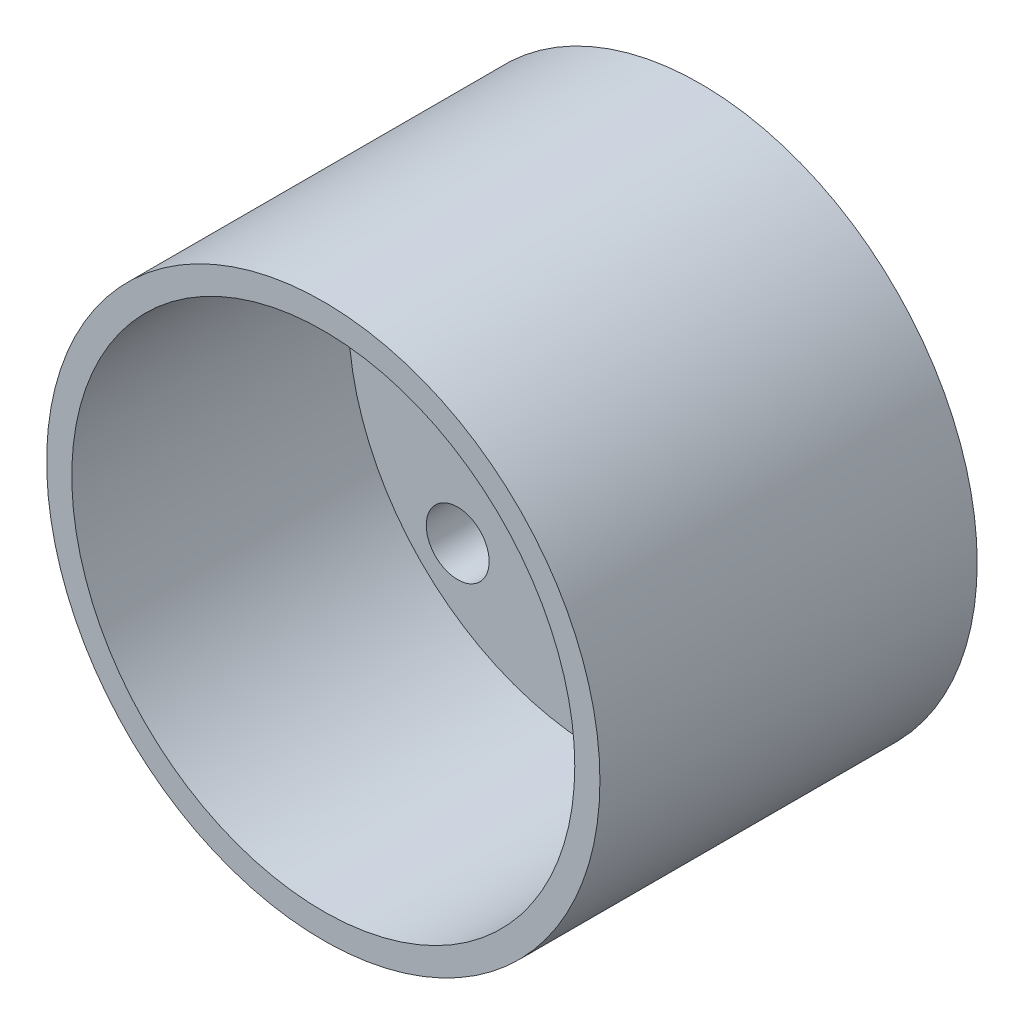
SolidWorks part; units mm, degrees
ref_plane "Front Plane" through (0, 0, 0) normal (0, 0, 1) x (1, 0, 0)
ref_plane "Top Plane" through (0, 0, 0) normal (0, 1, 0) x (1, 0, 0)
ref_plane "Right Plane" through (0, 0, 0) normal (1, 0, 0) x (0, 0, -1)
sketch "Sketch1" plane through (0, 0, 0) normal (0, 0, 1) x (1, 0, 0)
  circle A0 centre (0, 0) radius 11
  dimension "D1" = 22
extrude "Boss-Extrude1" add sketch "Sketch1" along normal blind 15
sketch "Sketch3" plane through (0, 0, 15) normal (0, 0, 1) x (1, 0, 0)
  circle A0 centre (0, 0) radius 10
  dimension "D1" = 20
extrude "Cut-Extrude1" cut sketch "Sketch3" against normal blind 11
sketch "Sketch4" plane through (0, 0, 0) normal (0, 0, -1) x (-1, 0, 0)
  circle A0 centre (0, 0) radius 4.15
  circle A1 centre (0, 8) radius 1.25
  circle A2 centre (5.6569, 5.6569) radius 1.25
  circle A3 centre (8, 0) radius 1.25
  circle A4 centre (5.6569, -5.6569) radius 1.25
  circle A5 centre (0, -8) radius 1.25
  circle A6 centre (-5.6569, -5.6569) radius 1.25
  circle A7 centre (-8, 0) radius 1.25
  circle A8 centre (-5.6569, 5.6569) radius 1.25
  point P22 (0, 0)
  dimension "D1" = 8.3
  dimension "D2" = 2.5
  dimension "D3" = 8
  dimension "D4" = 8
extrude "Cut-Extrude2" cut sketch "Sketch4" against normal blind 11
